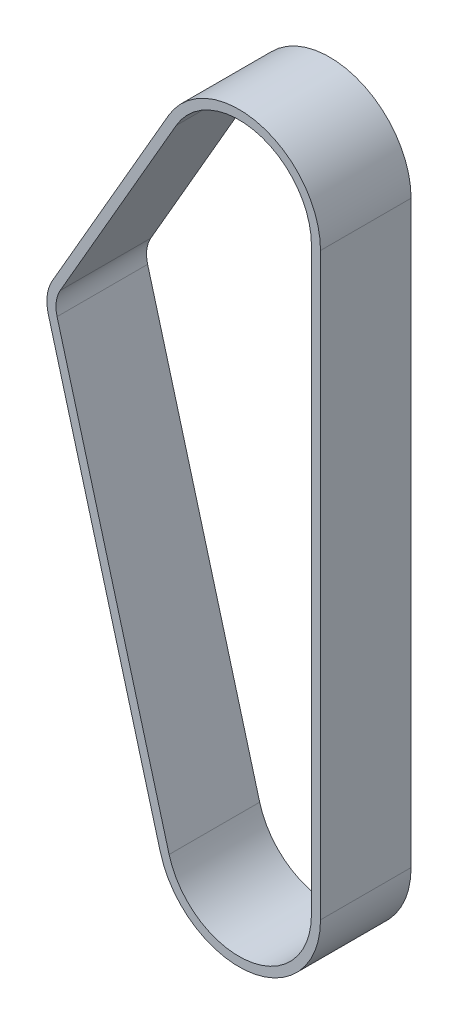
SolidWorks part; units mm, degrees
material "Rubber"
ref_plane "Front Plane" through (0, 0, 0) normal (0, 0, 1) x (1, 0, 0)
ref_plane "Top Plane" through (0, 0, 0) normal (0, 1, 0) x (1, 0, 0)
ref_plane "Right Plane" through (0, 0, 0) normal (1, 0, 0) x (0, 0, -1)
sketch "Sketch1" plane through (0, 0, 0) normal (0, 0, 1) x (1, 0, 0)
  line L0 (0, 0) -> (-50.1301, 0) construction
  line L1 (40, 320) -> (40, 0)
  line L2 (-98.7054, 229.0372) -> (-34.641, 340)
  line L3 (-40, 0) -> (-40, 21.2734) construction
  line L4 (-100.4305, 215.6722) -> (-38.5841, -10.5485)
  line L5 (0, 320) -> (-75.902, 320) construction
  line L6 (-40, 320) -> (-40, 297.9363) construction
  line L7 (-103.0356, 231.5372) -> (-38.9711, 342.5)
  line L8 (-105.2535, 214.3536) -> (-43.4071, -11.8671)
  line L9 (45, 320) -> (45, 0)
  line L10 (-100.8705, 230.2872) -> (-36.8061, 341.25) construction
  line L11 (42.5, 320) -> (42.5, 0) construction
  line L12 (-102.842, 215.0129) -> (-40.9956, -11.2078) construction
  arc A0 (-98.7054, 229.0372) -> (-100.4305, 215.6722) centre (-83.55, 220.2872) ccw
  arc A1 (40, 320) -> (-34.641, 340) centre (0, 320) ccw
  arc A2 (-38.5841, -10.5485) -> (40, 0) centre (0, 0) ccw
  arc A3 (45, 320) -> (-38.9711, 342.5) centre (0, 320) ccw
  arc A4 (-103.0356, 231.5372) -> (-105.2535, 214.3536) centre (-83.55, 220.2872) ccw
  arc A5 (-43.4071, -11.8671) -> (45, 0) centre (0, 0) ccw
  arc A6 (42.5, 320) -> (-36.8061, 341.25) centre (0, 320) ccw construction
  arc A7 (-40.9956, -11.2078) -> (42.5, 0) centre (0, 0) ccw construction
  arc A8 (-100.8705, 230.2872) -> (-102.842, 215.0129) centre (-83.55, 220.2872) ccw construction
  dimension "D1" = 80
  dimension "D3" = 35
  dimension "D4" = 320
  dimension "D5" = 123.55
  dimension "D7" = 2.5
  dimension "D8" = 931.9012
  dimension "D2" = 30
  dimension "D6" = 5
extrude "Boss-Extrude1" add sketch "Sketch1" along normal blind 50
